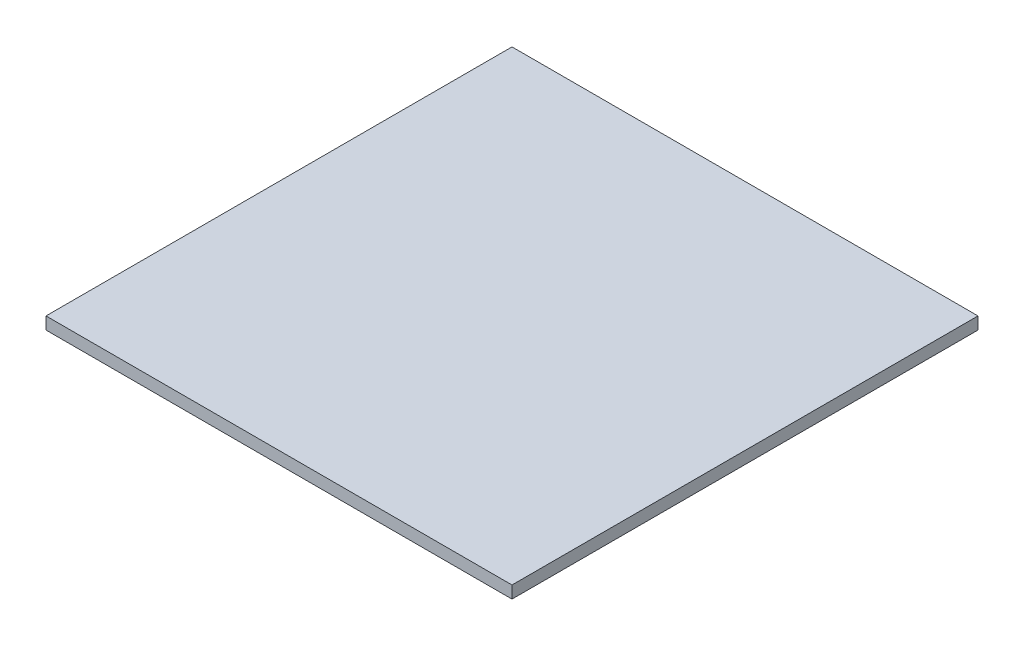
SolidWorks part; units mm, degrees
ref_plane "Front Plane" through (0, 0, 0) normal (0, 0, 1) x (1, 0, 0)
ref_plane "Top Plane" through (0, 0, 0) normal (0, 1, 0) x (1, 0, 0)
ref_plane "Right Plane" through (0, 0, 0) normal (1, 0, 0) x (0, 0, -1)
sketch "Sketch1" plane through (0, 0, 0) normal (0, 1, 0) x (1, 0, 0)
  line L1 (0, 0) -> (603.25, 0)
  line L2 (0, 0) -> (0, 603.25)
  line L3 (0, 603.25) -> (603.25, 603.25)
  line L4 (603.25, 0) -> (603.25, 603.25)
  dimension "D1" = 603.25
  dimension "D2" = 603.25
extrude "Boss-Extrude1" add sketch "Sketch1" along normal blind 15.875
